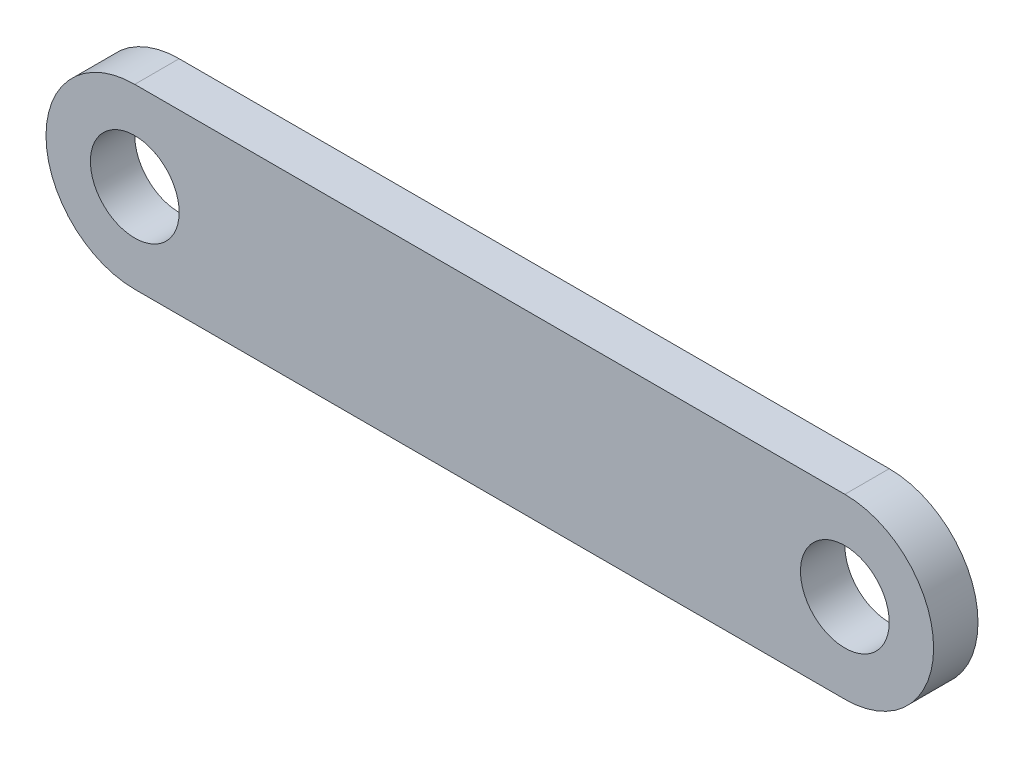
SolidWorks part; units mm, degrees
ref_plane "Front Plane" through (0, 0, 0) normal (0, 0, 1) x (1, 0, 0)
ref_plane "Top Plane" through (0, 0, 0) normal (0, 1, 0) x (1, 0, 0)
ref_plane "Right Plane" through (0, 0, 0) normal (1, 0, 0) x (0, 0, -1)
sketch "Sketch1" plane through (0, 0, 0) normal (0, 0, 1) x (1, 0, 0)
  line L0 (0, 0) -> (32, 0) construction
  line L1 (0, 4) -> (32, 4)
  line L2 (0, -4) -> (32, -4)
  arc A0 (0, 4) -> (0, -4) centre (0, 0) ccw
  arc A1 (32, -4) -> (32, 4) centre (32, 0) ccw
  circle A2 centre (0, 0) radius 2
  circle A3 centre (32, 0) radius 2
  point P3 (16, 0)
  dimension "D3" = 4
  dimension "D4" = 4
  dimension "D1" = 8
  dimension "D2" = 32
extrude "Boss-Extrude1" add sketch "Sketch1" along normal mid plane 2
